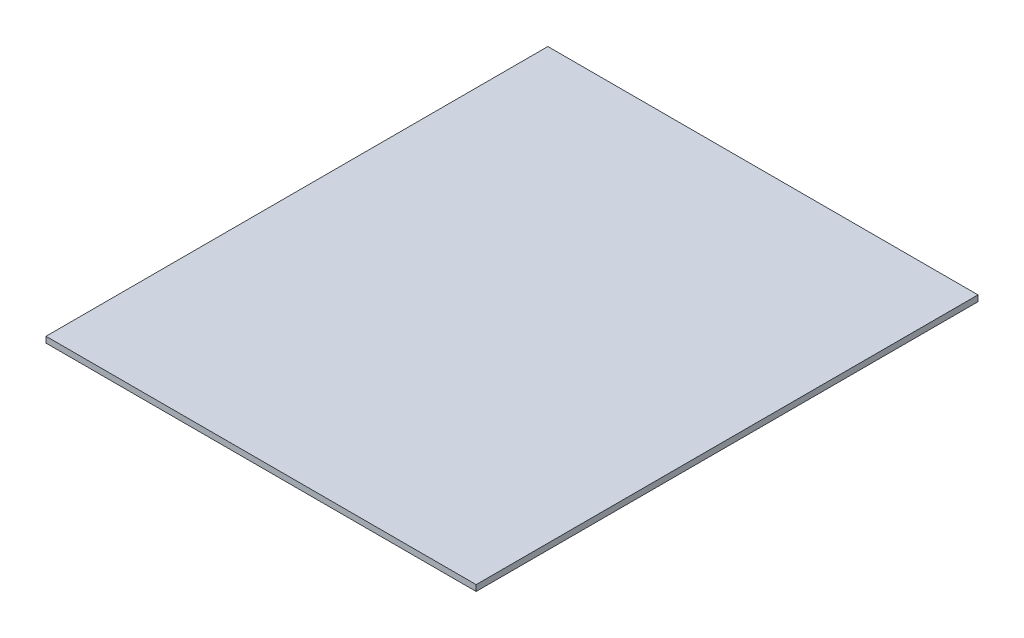
SolidWorks part; units mm, degrees
ref_plane "Front Plane" through (0, 0, 0) normal (0, 0, 1) x (1, 0, 0)
ref_plane "Top Plane" through (0, 0, 0) normal (0, 1, 0) x (1, 0, 0)
ref_plane "Right Plane" through (0, 0, 0) normal (1, 0, 0) x (0, 0, -1)
sketch "Sketch1" plane through (0, 0, 0) normal (0, 1, 0) x (1, 0, 0)
  line L1 (-114.3, 133.35) -> (114.3, 133.35)
  line L2 (-114.3, 133.35) -> (-114.3, -133.35)
  line L3 (-114.3, -133.35) -> (114.3, -133.35)
  line L4 (114.3, 133.35) -> (114.3, -133.35)
  line L5 (-114.3, 133.35) -> (114.3, -133.35) construction
  line L6 (-114.3, -133.35) -> (114.3, 133.35) construction
  point P0 (0, 0)
  dimension "D1" = 228.6
  dimension "D2" = 266.7
extrude "Boss-Extrude1" add sketch "Sketch1" along normal blind 3.175
